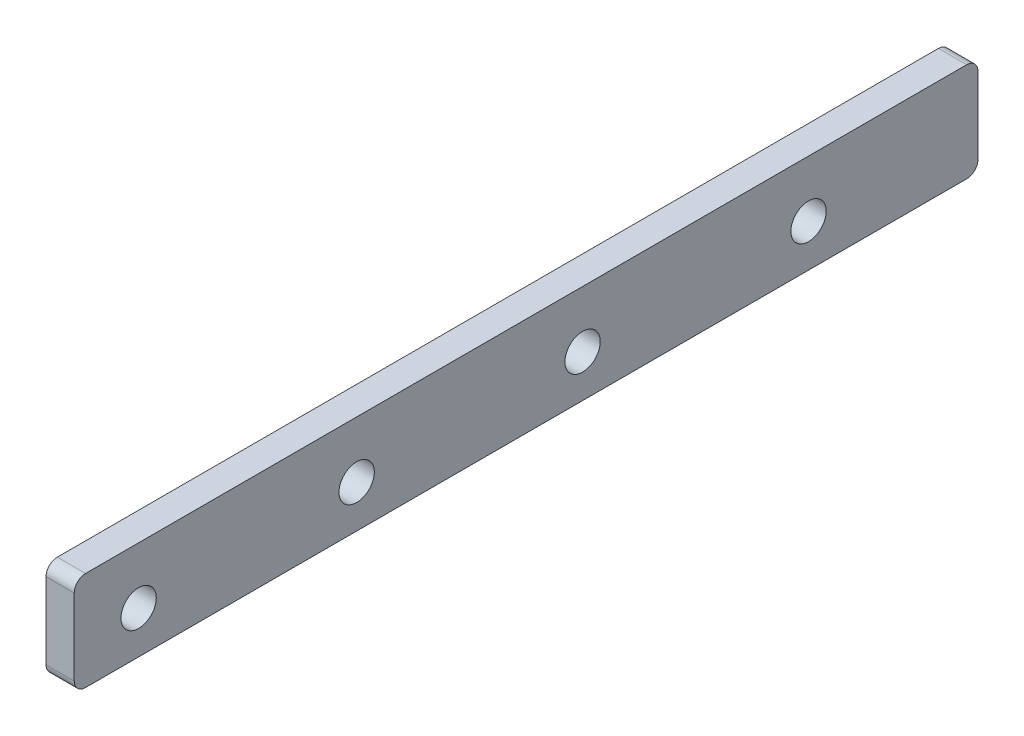
SolidWorks part; units mm, degrees
material "6061-T6 (SS)"
ref_plane "Front Plane" through (0, 0, 0) normal (0, 0, 1) x (1, 0, 0)
ref_plane "Top Plane" through (0, 0, 0) normal (0, 1, 0) x (1, 0, 0)
ref_plane "Right Plane" through (0, 0, 0) normal (1, 0, 0) x (0, 0, -1)
sketch "Sketch1" plane through (0, 0, 0) normal (1, 0, 0) x (0, 0, -1)
  line L0 (0, 12.7) -> (155.575, 12.7) construction
  line L1 (0, 0) -> (155.575, 0)
  line L2 (0, 0) -> (0, 25.4)
  line L3 (0, 25.4) -> (155.575, 25.4)
  line L4 (155.575, 0) -> (155.575, 25.4)
  line L5 (-47.625, 12.7) -> (0, 12.7) construction
  line L6 (0, 25.4) -> (-47.625, 25.4)
  line L7 (0, 25.4) -> (0, 0)
  line L8 (0, 0) -> (-47.625, 0)
  line L9 (-47.625, 25.4) -> (-47.625, 0)
  line L10 (-47.625, 3.175) -> (155.575, 3.175)
  circle A0 centre (15.875, 12.7) radius 3.9688
  circle A1 centre (66.675, 12.7) radius 3.9687
  circle A2 centre (117.475, 12.7) radius 3.9688
  circle A3 centre (-33.147, 12.7) radius 3.9688
  point P18 (155.575, 3.6753)
  dimension "D3" = 7.9375
  dimension "D8" = 7.9375
  dimension "D1" = 50.8
  dimension "D2" = 50.8
  dimension "D4" = 15.875
  dimension "D5" = 38.1
  dimension "D6" = 12.7
  dimension "D7" = 49.022
  dimension "D9" = 47.625
  dimension "D10" = 3.175
extrude "Boss-Extrude1" add sketch "Sketch1" along normal blind 6.35 contours L6 L9 L8 L2 A3 | L1 L4 L3 L2 A2 A1 A0
fillet "Fillet1" radius 2.54 4 edges at (3.175, 25.4, -155.575) (3.175, 25.4, 47.625) (3.175, 3.175, 47.625) (3.175, 3.175, -155.575)
